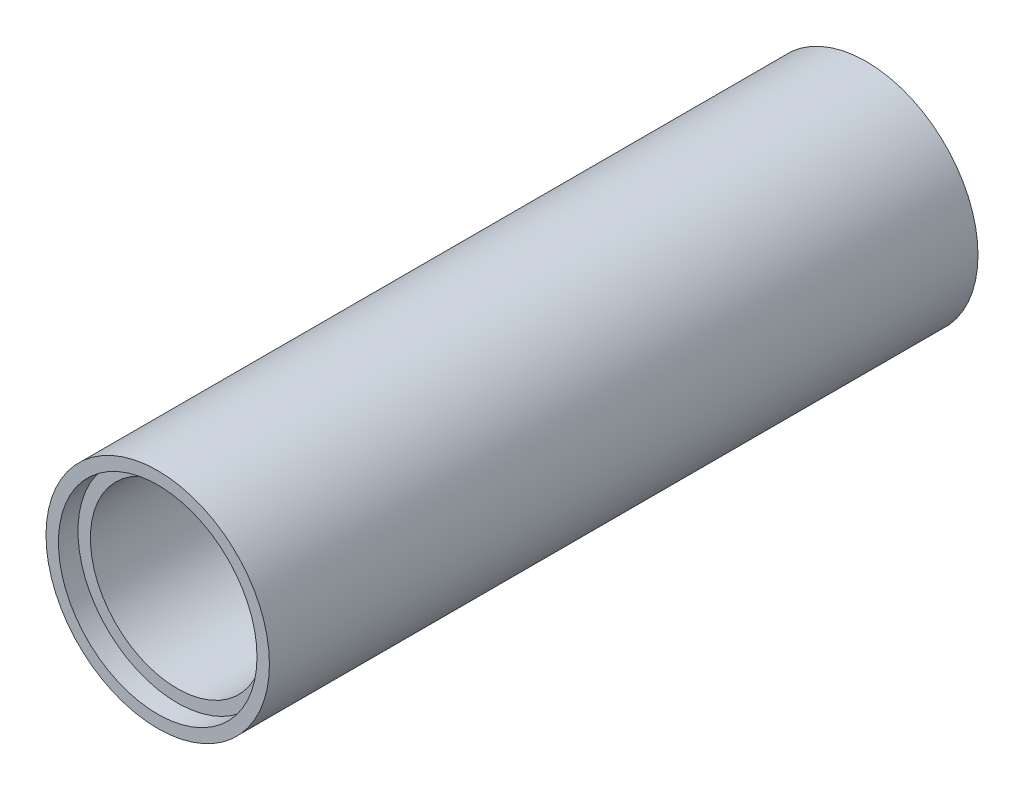
SolidWorks part; units mm, degrees
ref_plane "Front Plane" through (0, 0, 0) normal (0, 0, 1) x (1, 0, 0)
ref_plane "Top Plane" through (0, 0, 0) normal (0, 1, 0) x (1, 0, 0)
ref_plane "Right Plane" through (0, 0, 0) normal (1, 0, 0) x (0, 0, -1)
sketch "Sketch1" plane through (0, 0, 0) normal (0, 0, 1) x (1, 0, 0)
  circle A0 centre (0, 0) radius 57.15
  circle A1 centre (0, 0) radius 44.45
  dimension "D1" = 114.3
  dimension "D2" = 88.9
extrude "Boss-Extrude1" add sketch "Sketch1" along normal blind 362.5
sketch "Sketch2" plane through (0, 0, 362.5) normal (0, 0, 1) x (1, 0, 0)
  circle A0 centre (0, 0) radius 50.8
  circle A1 centre (0, 0) radius 44.45 construction
  circle A2 centre (0, 0) radius 44.45
  dimension "D1" = 101.6
extrude "Cut-Extrude1" cut sketch "Sketch2" against normal blind 10
